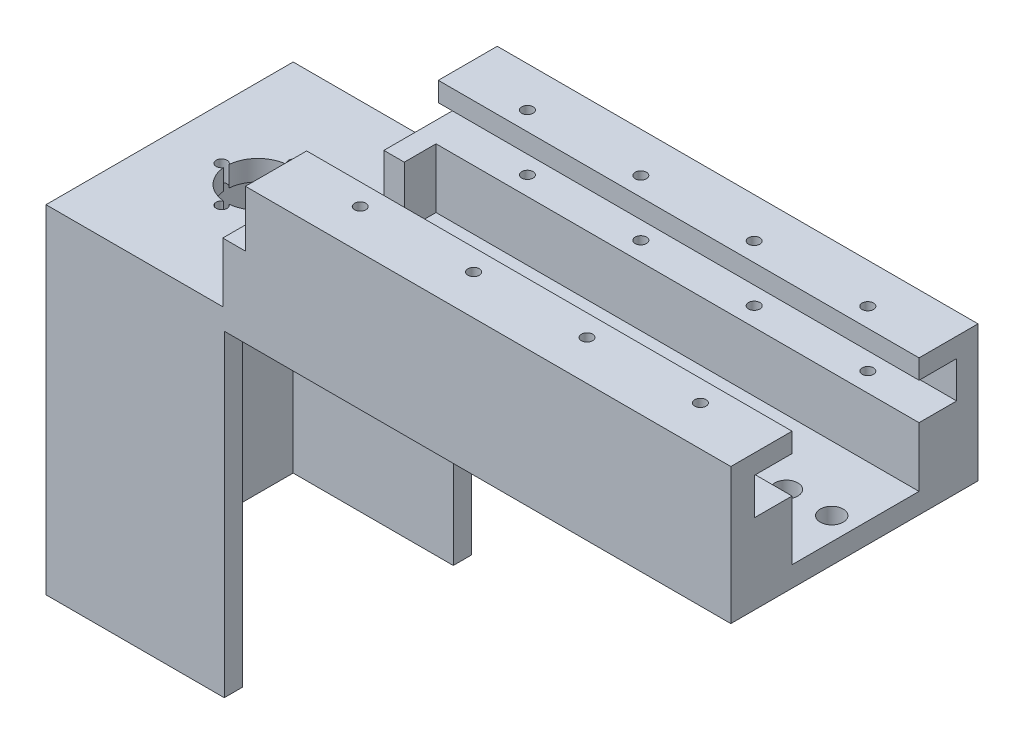
SolidWorks part; units mm, degrees
ref_plane "Front Plane" through (0, 0, 0) normal (0, 0, 1) x (1, 0, 0)
ref_plane "Top Plane" through (0, 0, 0) normal (0, 1, 0) x (1, 0, 0)
ref_plane "Right Plane" through (0, 0, 0) normal (1, 0, 0) x (0, 0, -1)
sketch "Sketch4" plane through (0, 0, 0) normal (0, 0, 1) x (1, 0, 0)
  line L1 (-89.891, -20.3228) -> (16.109, -20.3228)
  line L2 (-89.891, -20.3228) -> (-89.891, -50.3228)
  line L3 (-89.891, -50.3228) -> (16.109, -50.3228)
  line L4 (16.109, -20.3228) -> (16.109, -50.3228)
  dimension "D1" = 30
  dimension "D2" = 106
extrude "Boss-Extrude2" add sketch "Sketch4" against normal blind 13
sketch "Sketch25" plane through (0, 0, 0) normal (0, 0, 1) x (1, 0, 0)
  line L0 (-89.891, -20.3228) -> (-89.891, -50.3228) construction
  line L1 (-89.891, -24.6013) -> (16.109, -24.6013)
  line L2 (-89.891, -24.6013) -> (-89.891, -32.7013)
  line L3 (-89.891, -32.7013) -> (16.109, -32.7013)
  line L4 (16.109, -24.6013) -> (16.109, -32.7013)
  line L5 (16.109, -50.3228) -> (16.109, -20.3228) construction
extrude "Cut-Extrude3" cut sketch "Sketch25" against normal blind 8.3 and the other way through all
hole_wizard "M3x0.5 Tapped Hole1" positions "3DSketch1" profile "Sketch27" tap size "M3x0.5" standard "ANSI Metric" end condition through all
sketch3d "3DSketch1"
  line L0 (16.109, -20.3228, -13) -> (16.109, -20.3228, 0) construction
  line L2 (16.109, -20.3228, 0) -> (-89.891, -20.3228, 0) construction
  line L3 (-89.891, -20.3228, -13) -> (-89.891, -20.3228, 0) construction
  point P0 (-74.391, -20.3228, -4.15)
  point P2 (-49.391, -20.3228, -4.15)
  point P4 (0.609, -20.3228, -4.2057)
  point P6 (-24.391, -20.3228, -4.15)
  dimension "D1" = 15.5
  dimension "D2" = 25
  dimension "D5" = 4.15
  dimension "D6" = 4.15
  dimension "D7" = 4.15
  dimension "D8" = 25
  dimension "D9" = 25
  dimension "D10" = 15.5001
cosmetic thread "Hole Thread2" parameters "D1"=6, "D2"=3
cosmetic thread "Hole Thread3" parameters "D1"=6, "D2"=3
cosmetic thread "Hole Thread4" parameters "D1"=6, "D2"=3
cosmetic thread "Hole Thread5" parameters "D1"=6, "D2"=3
sketch "Sketch27" plane through (-74.391, -20.3228, -4.15) normal (1, 0, 0) x (0, 0, 1)
  line L0 (0, 0) -> (0, 30)
  line L1 (0, 30) -> (1.25, 30)
  line L2 (1.25, 30) -> (1.25, 0)
  line L5 (1.25, 0) -> (0, 0)
  line L11 (0, -6.35) -> (0, 107.95) construction
  dimension "Thru Tap Drill Dia." = 2.5
  dimension "Thru Tap Drill Depth" = 30
sketch "Sketch28" plane through (0, 0, 0) normal (0, 0, 1) x (1, 0, 0)
  line L0 (-89.891, -32.7013) -> (-89.891, -50.3228) construction
  line L1 (-89.891, -45.8228) -> (16.109, -45.8228)
  line L2 (-89.891, -45.8228) -> (-89.891, -50.3228)
  line L3 (-89.891, -50.3228) -> (16.109, -50.3228)
  line L4 (16.109, -45.8228) -> (16.109, -50.3228)
  dimension "D1" = 4.5
extrude "Boss-Extrude3" add sketch "Sketch28" along normal blind 41.5
sketch "Sketch32" plane through (-89.891, 0, 0) normal (-1, 0, 0) x (0, 0, 1)
  line L1 (0, -45.8228) -> (41.5, -45.8228)
  line L2 (0, -45.8228) -> (0, -50.3228)
  line L3 (0, -50.3228) -> (41.5, -50.3228)
  line L4 (41.5, -45.8228) -> (41.5, -50.3228)
extrude "Boss-Extrude10" add sketch "Sketch32" along normal blind 5
sketch "Sketch33" plane through (-89.891, 0, 0) normal (-1, 0, 0) x (0, 0, 1)
  line L1 (0, -32.7013) -> (-13, -32.7013)
  line L2 (0, -32.7013) -> (0, -50.3228)
  line L3 (0, -50.3228) -> (-13, -50.3228)
  line L4 (-13, -32.7013) -> (-13, -50.3228)
extrude "Boss-Extrude12" add sketch "Sketch33" along normal blind 5
sketch "Sketch34" plane through (0, 0, 0) normal (0, 0, 1) x (1, 0, 0)
  line L0 (16.109, -45.8228) -> (-94.891, -45.8228) construction
  line L1 (-94.891, -32.7013) -> (-90.3922, -32.7013)
  line L2 (-94.891, -32.7013) -> (-94.891, -45.8228)
  line L3 (-94.891, -45.8228) -> (-90.3922, -45.8228)
  line L4 (-90.3922, -32.7013) -> (-90.3922, -45.8228)
extrude "Boss-Extrude13" add sketch "Sketch34" along normal blind 7
sketch "Sketch35" plane through (-94.891, 0, 0) normal (-1, 0, 0) x (0, 0, 1)
  line L1 (41.5, -45.8228) -> (-13, -45.8228)
  line L2 (41.5, -45.8228) -> (41.5, -50.3228)
  line L3 (41.5, -50.3228) -> (-13, -50.3228)
  line L4 (-13, -45.8228) -> (-13, -50.3228)
extrude "Boss-Extrude14" add sketch "Sketch35" along normal blind 40
sketch "Sketch36" plane through (0, -45.8228, 0) normal (0, 1, 0) x (1, 0, 0)
  line L0 (16.109, -41.5) -> (-134.891, -41.5) construction
  line L1 (-90.9181, -41.5) -> (-95.9181, -41.5)
  line L2 (-90.9181, -41.5) -> (-90.9181, -21.5)
  line L3 (-90.9181, -21.5) -> (-95.9181, -21.5)
  line L4 (-95.9181, -41.5) -> (-95.9181, -21.5)
  dimension "D1" = 5
  dimension "D2" = 20
extrude "Boss-Extrude15" add sketch "Sketch36" along normal blind 13.12 contours L2 L3 L4 L1
hole_wizard "#8 (0.199) Diameter Hole1" positions "3DSketch3" profile "Sketch38" hole size "#8" standard "Progressive" end condition through all
sketch3d "3DSketch3"
  line L0 (16.109, -45.8228, 41.5) -> (-90.9181, -45.8228, 41.5) construction
  line L1 (16.109, -45.8228, 41.5) -> (16.109, -45.8228, 0) construction
  point P0 (-80.6691, -45.8228, 14.25)
  point P2 (11.109, -45.8228, 14.25)
  point P4 (1.109, -45.8228, 14.25)
  point P6 (-70.6691, -45.8228, 14.25)
  dimension "D1" = 27.25
  dimension "D2" = 27.25
  dimension "D3" = 27.25
  dimension "D4" = 27.25
  dimension "D5" = 10
  dimension "D6" = 10
  dimension "D7" = 5
sketch "Sketch38" plane through (-80.6691, -45.8228, 14.25) normal (1, 0, 0) x (0, 0, 1)
  line L0 (0, 0) -> (0, 4.5)
  line L1 (0, 4.5) -> (2.5273, 4.5)
  line L2 (2.5273, 4.5) -> (2.5273, 0)
  line L5 (2.5273, 0) -> (0, 0)
  line L11 (0, -6.35) -> (0, 107.95) construction
  dimension "Thru Hole Dia." = 5.0546
  dimension "Thru Hole Depth" = 4.5
sketch "Sketch39" plane through (0, -45.8228, 0) normal (0, 1, 0) x (1, 0, 0)
  line L1 (-95.9181, -41.5) -> (-95.9181, -21.5) construction
  line L2 (-134.891, -41.5) -> (-134.891, 13) construction
  line L3 (-134.891, 13) -> (-94.891, 13) construction
  circle A0 centre (-115.4181, -14.25) radius 7
  dimension "D1" = 19.5
  dimension "D2" = 19.4729
  dimension "D3" = 27.25
extrude "Cut-Extrude4" cut sketch "Sketch39" against normal blind 10 contours A0
hole_wizard "M2 Clearance Hole1" positions "3DSketch4" profile "Sketch40" hole size "M2" standard "ANSI Metric" end condition through all
sketch3d "3DSketch4"
  line L0 (-134.891, -45.8228, 41.5) -> (-134.891, -45.8228, -13) construction
  line L1 (-95.9181, -45.8228, 41.5) -> (-134.891, -45.8228, 41.5) construction
  line L3 (-95.9181, -45.8228, 41.5) -> (-95.9181, -45.8228, 21.5) construction
  point P0 (-107.4181, -45.8228, 14.25)
  point P2 (-115.421, -45.8228, 22.25)
  point P4 (-115.421, -45.8228, 6.25)
  point P6 (-123.4181, -45.8228, 14.25)
  point P19 (-115.4046, -45.8228, 41.5)
  dimension "D1" = 19.47
  dimension "D2" = 19.47
  dimension "D3" = 16
  dimension "D4" = 27.25
  dimension "D5" = 27.25
  dimension "D6" = 19.25
  dimension "D7" = 16
  dimension "D8" = 11.5
  dimension "D9" = 11.4729
sketch "Sketch40" plane through (-107.4181, -45.8228, 14.25) normal (1, 0, 0) x (0, 0, 1)
  line L0 (0, 0) -> (0, 4.5)
  line L1 (0, 4.5) -> (1.2, 4.5)
  line L2 (1.2, 4.5) -> (1.2, 0)
  line L5 (1.2, 0) -> (0, 0)
  line L11 (0, -6.35) -> (0, 107.95) construction
  dimension "Thru Hole Dia." = 2.4
  dimension "Thru Hole Depth" = 4.5
sketch "Sketch43" plane through (0, -50.3228, 0) normal (0, -1, 0) x (-1, 0, 0)
  line L0 (134.891, -41.5) -> (-16.109, -41.5) construction
  line L1 (95.5862, -41.5) -> (134.891, -41.5)
  line L2 (95.5862, -41.5) -> (95.5862, -37.5)
  line L3 (95.5862, -37.5) -> (134.891, -37.5)
  line L4 (134.891, -41.5) -> (134.891, -37.5)
  line L5 (134.891, 13) -> (134.891, -41.5) construction
  line L6 (134.891, 13) -> (-16.109, 13) construction
  line L7 (134.891, -37.5) -> (130.891, -37.5)
  line L8 (134.891, -37.5) -> (134.891, 13)
  line L9 (134.891, 13) -> (130.891, 13)
  line L10 (130.891, -37.5) -> (130.891, 13)
  line L12 (95.5862, 13) -> (130.891, 13)
  line L13 (95.5862, 13) -> (95.5862, 9)
  line L14 (95.5862, 9) -> (130.891, 9)
  line L15 (130.891, 13) -> (130.891, 9)
  line M8 (-16.109, -41.5) -> (134.891, -41.5)
  line M9 (134.891, -41.5) -> (134.891, 13)
  line M10 (134.891, 13) -> (-16.109, 13)
  dimension "D1" = 4
  dimension "D2" = 4
  dimension "D3" = 4
extrude "Boss-Extrude16" add sketch "Sketch43" along normal blind 70 contours L3 L2 M8 M9 | L10 L3 M9 M10 | L15 L14 L13 L12
sketch "Sketch44" plane through (0, -45.8228, 0) normal (0, 1, 0) x (1, 0, 0)
  line L0 (16.109, -41.5) -> (16.109, 0) construction
  line L1 (-90.9181, -41.5) -> (16.109, -41.5)
  line L2 (-90.9181, -41.5) -> (-90.9181, -28)
  line L3 (-90.9181, -28) -> (16.109, -28)
  line L4 (16.109, -41.5) -> (16.109, -28)
  point P7 (-118.8841, -49.0681)
  point P8 (-42.4113, -14.1771)
  dimension "D1" = 13.5
extrude "Boss-Extrude17" add sketch "Sketch44" along normal blind 25.5
sketch "Sketch47" plane through (0, 0, 28) normal (0, 0, -1) x (-1, 0, 0)
  line L0 (-16.109, -20.3228) -> (-16.109, -45.8228) construction
  line L1 (-16.109, -32.7028) -> (90.9181, -32.7028)
  line L2 (-16.109, -32.7028) -> (-16.109, -24.6028)
  line L3 (-16.109, -24.6028) -> (90.9181, -24.6028)
  line L4 (90.9181, -32.7028) -> (90.9181, -24.6028)
  line L5 (90.9181, -20.3228) -> (90.9181, -32.7028) construction
  point P8 (86.6192, -23.1225)
  point P9 (20.9745, -22.0682)
  point P10 (-17.4811, -26.3808)
  point P11 (-12.09, -31.216)
  dimension "D1" = 8.1
  dimension "D2" = 4.28
extrude "Cut-Extrude5" cut sketch "Sketch47" against normal blind 8.3 contours L3 L4 L1 L2
hole_wizard "M3x0.5 Tapped Hole2" positions "3DSketch5" profile "Sketch49" tap size "M3x0.5" standard "ANSI Metric"
sketch3d "3DSketch5"
  line L0 (16.109, -20.3228, 41.5) -> (16.109, -20.3228, 28) construction
  line L1 (-90.9181, -20.3228, 41.5) -> (16.109, -20.3228, 41.5) construction
  point P0 (-74.391, -20.3228, 32.71)
  point P2 (-49.391, -20.3228, 32.71)
  point P4 (-24.391, -20.3228, 32.71)
  point P6 (0.609, -20.3228, 32.71)
  dimension "D1" = 15.5
  dimension "D2" = 8.79
  dimension "D3" = 8.79
  dimension "D4" = 25
  dimension "D5" = 8.79
  dimension "D6" = 25
  dimension "D7" = 25
  dimension "D8" = 8.79
cosmetic thread "Hole Thread6" parameters "D2"=3
cosmetic thread "Hole Thread7" parameters "D2"=3
cosmetic thread "Hole Thread8" parameters "D2"=3
cosmetic thread "Hole Thread9" parameters "D2"=3
sketch "Sketch49" plane through (-74.391, -20.3228, 32.71) normal (1, 0, 0) x (0, 0, 1)
  line L0 (0, 0) -> (0, 30.7501)
  line L1 (0, 30.7501) -> (1.25, 29.999)
  line L2 (1.25, 29.999) -> (1.25, 0)
  line L5 (1.25, 0) -> (0, 0)
  line L10 (0, 30.7501) -> (-1.25, 29.999) construction
  line L11 (0, -6.35) -> (0, 107.95) construction
  dimension "Tap Drill Dia." = 2.5
  dimension "Tap Drill Depth" = 29.999
  dimension "Drill Angle" = 118
